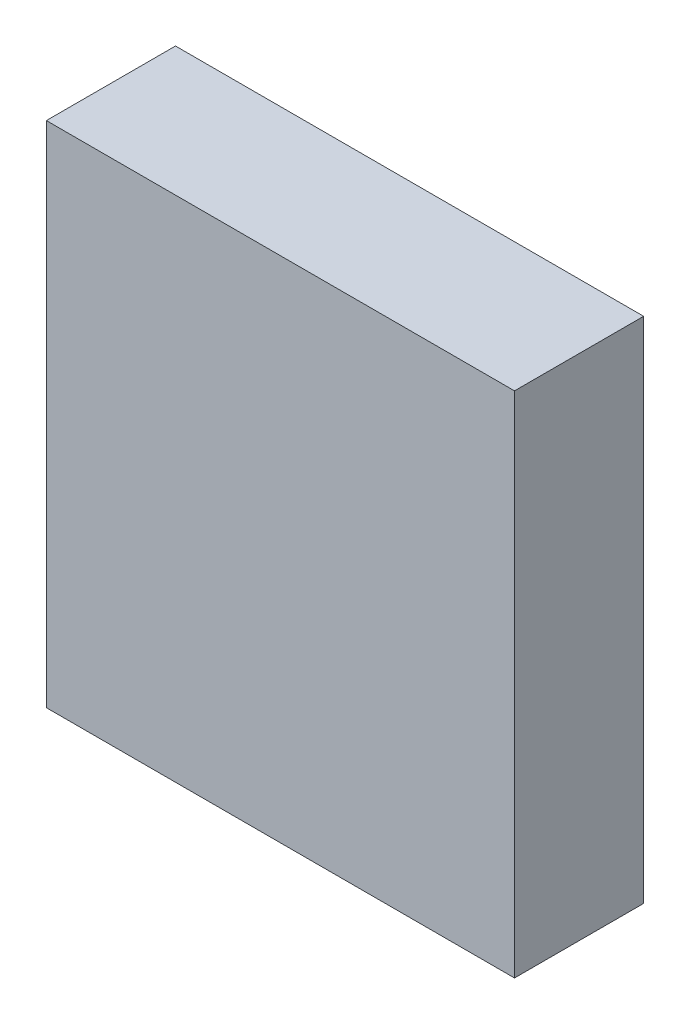
SolidWorks part; units mm, degrees
ref_plane "Front Plane" through (0, 0, 0) normal (0, 0, 1) x (1, 0, 0)
ref_plane "Top Plane" through (0, 0, 0) normal (0, 1, 0) x (1, 0, 0)
ref_plane "Right Plane" through (0, 0, 0) normal (1, 0, 0) x (0, 0, -1)
sketch "Sketch1" plane through (0, 0, 0) normal (0, 0, 1) x (1, 0, 0)
  line L1 (0, 0) -> (58, 0)
  line L2 (0, 0) -> (0, 63)
  line L3 (0, 63) -> (58, 63)
  line L4 (58, 0) -> (58, 63)
  dimension "D1" = 58
  dimension "D2" = 63
extrude "Boss-Extrude1" add sketch "Sketch1" along normal blind 16
sketch "Sketch2" plane through (0, 0, 0) normal (-1, 0, 0) x (0, 0, 1)
  line L0 (16, 63) -> (0, 63) construction
  line L1 (0, 50.3) -> (4.7625, 50.3)
  line L2 (0, 50.3) -> (0, 43.95)
  line L3 (0, 43.95) -> (4.7625, 43.95)
  line L4 (4.7625, 50.3) -> (4.7625, 43.95)
  line L5 (0, 63) -> (0, 0) construction
  dimension "D1" = 12.7
  dimension "D2" = 6.35
  dimension "D3" = 4.7625
extrude "Boss-Extrude2" add sketch "Sketch2" along normal blind 6.35
